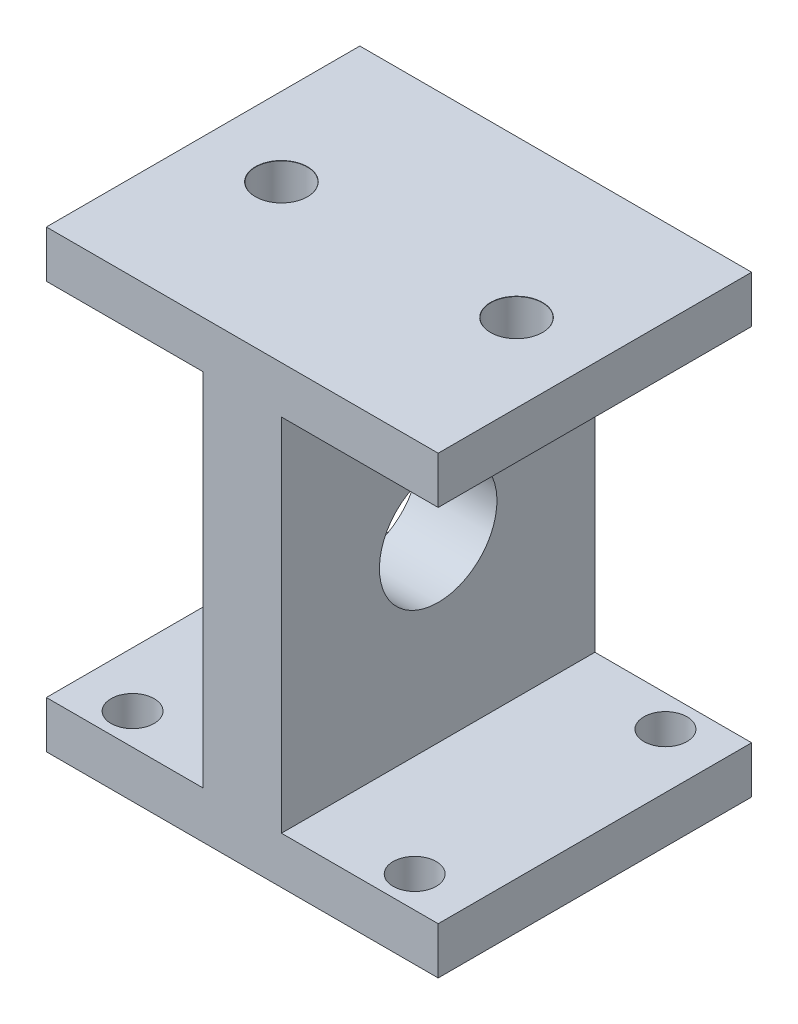
SolidWorks part; units mm, degrees
ref_plane "前视基准面" through (0, 0, 0) normal (0, 0, 1) x (1, 0, 0)
ref_plane "上视基准面" through (0, 0, 0) normal (0, 1, 0) x (1, 0, 0)
ref_plane "右视基准面" through (0, 0, 0) normal (1, 0, 0) x (0, 0, -1)
sketch "草图1" plane through (0, 0, 0) normal (0, 0, 1) x (1, 0, 0)
  line L1 (-25, 29) -> (25, 29)
  line L2 (-25, 29) -> (-25, -29)
  line L3 (-25, -29) -> (25, -29)
  line L4 (25, 29) -> (25, -29)
  line L5 (-25, 29) -> (25, -29) construction
  line L6 (-25, -29) -> (25, 29) construction
  point P0 (0, 0)
  dimension "D1" = 50
  dimension "D2" = 58
extrude "凸台-拉伸1" add sketch "草图1" along normal blind 40
sketch "草图2" plane through (0, 0, 40) normal (0, 0, 1) x (1, 0, 0)
  line L0 (0, 32.4691) -> (0, -41.8295) construction
  line L1 (-37.7928, 23) -> (-5, 23)
  line L2 (-37.7928, 23) -> (-37.7928, -23)
  line L3 (-37.7928, -23) -> (-5, -23)
  line L4 (-5, 23) -> (-5, -23)
  line L5 (25, 29) -> (-25, 29) construction
  line L6 (-25, -29) -> (25, -29) construction
  line L7 (5, 23) -> (5, -23)
  line L8 (37.7928, -23) -> (5, -23)
  line L9 (37.7928, 23) -> (37.7928, -23)
  line L10 (37.7928, 23) -> (5, 23)
  point P7 (0, -41.8295)
  dimension "D1" = 6
  dimension "D2" = 6
  dimension "D3" = 5
extrude "切除-拉伸1" cut sketch "草图2" against normal blind 60
sketch "草图3" plane through (-5, 0, 0) normal (-1, 0, 0) x (0, 0, 1)
  line L0 (20, 23) -> (20, -23) construction
  line L1 (0, 23) -> (40, 23) construction
  line L2 (0, -23) -> (40, -23) construction
  line L3 (40, 0) -> (-4.3503, 0) construction
  line L4 (40, -23) -> (40, 23) construction
  circle A0 centre (20, 0) radius 7.5
  point P8 (0, 0)
  point P14 (-4.3503, 0)
  point P15 (0, 0)
  dimension "D1" = 15
extrude "切除-拉伸2" cut sketch "草图3" against normal blind 35
sketch "草图4" plane through (0, -29, 0) normal (0, -1, 0) x (1, 0, 0)
  line L0 (25, 20) -> (18.4226, 20) construction
  line L1 (18, 36) -> (-18, 36)
  line L2 (18, 36) -> (18, 4)
  line L3 (18, 4) -> (-18, 4)
  line L4 (-18, 36) -> (-18, 4)
  line L5 (25, 40) -> (25, 0) construction
  line L6 (0, 40) -> (0, 37.4251) construction
  line L7 (-25, 40) -> (25, 40) construction
  dimension "D1" = 32
  dimension "D2" = 36
hole_wizard "M5 间隙槽口1" positions "草图5" profile "草图6" size "M5" standard "GB" slot yes
sketch "草图5" plane through (0, -29, 0) normal (0, -1, 0) x (-1, 0, 0)
  point P0 (-18, -4)
  point P3 (18, -4)
  point P6 (18, -36)
  point P9 (-18, -36)
sketch "草图6" plane through (18, -29, 4) normal (1, 0, 0) x (0, 0, -1)
  line L0 (0, 0) -> (0, 18.6524)
  line L1 (0, 18.6524) -> (2.75, 17)
  line L2 (2.75, 17) -> (2.75, 0.025)
  line L3 (2.75, 0.025) -> (2.775, 0)
  line L5 (2.775, 0) -> (0, 0)
  line L6 (-2.75, 0.025) -> (-2.775, 0) construction
  line L10 (0, 18.6524) -> (-2.75, 17) construction
  line L11 (0, -6.35) -> (0, 107.95) construction
  dimension "孔直径" = 5.5
  dimension "孔深度" = 17
  dimension "近端锥形沉头孔直径" = 5.55
  dimension "近端锥形沉头孔角度" = 90
  dimension "导头角度" = 118
sketch "草图7" plane through (0, 29, 0) normal (0, 1, 0) x (1, 0, 0)
  line L0 (25, -20) -> (31.4408, -20)
  line L1 (25, -40) -> (25, 0) construction
  line L2 (15, -20) -> (-15, -20)
  line L3 (0, 0) -> (0, -12.0604) construction
  line L4 (25, 0) -> (-25, 0) construction
  point P10 (0, 0)
  dimension "D1" = 30
hole_wizard "M6 间隙槽口1" positions "草图8" profile "草图9" size "M6" standard "GB" slot yes
sketch "草图8" plane through (0, 29, 0) normal (0, 1, 0) x (1, 0, 0)
  point P0 (-15, -20)
  point P3 (15, -20)
sketch "草图9" plane through (-15, 29, 20) normal (1, 0, 0) x (0, 0, 1)
  line L0 (0, 0) -> (0, 18.9828)
  line L1 (0, 18.9828) -> (3.3, 17)
  line L2 (3.3, 17) -> (3.3, 0.025)
  line L3 (3.3, 0.025) -> (3.325, 0)
  line L5 (3.325, 0) -> (0, 0)
  line L6 (-3.3, 0.025) -> (-3.325, 0) construction
  line L10 (0, 18.9828) -> (-3.3, 17) construction
  line L11 (0, -6.35) -> (0, 107.95) construction
  dimension "孔直径" = 6.6
  dimension "孔深度" = 17
  dimension "近端锥形沉头孔直径" = 6.65
  dimension "近端锥形沉头孔角度" = 90
  dimension "导头角度" = 118
